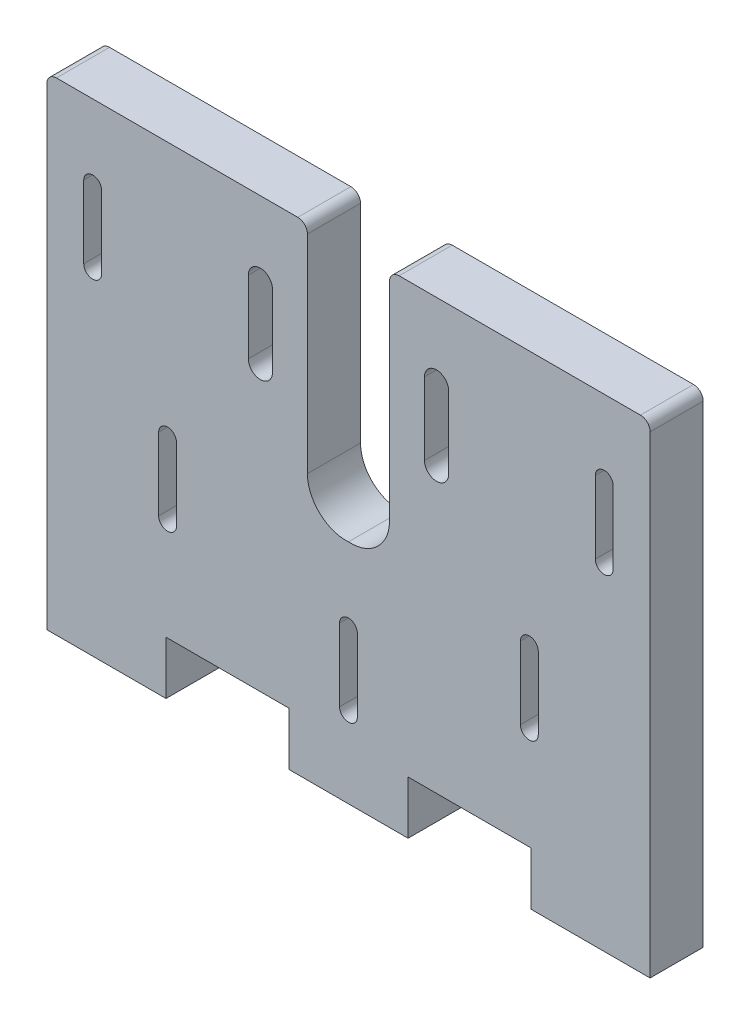
SolidWorks part; units mm, degrees
ref_plane "Front Plane" through (0, 0, 0) normal (0, 0, 1) x (1, 0, 0)
ref_plane "Top Plane" through (0, 0, 0) normal (0, 1, 0) x (1, 0, 0)
ref_plane "Right Plane" through (0, 0, 0) normal (1, 0, 0) x (0, 0, -1)
sketch "Sketch2" plane through (0, 0, 0) normal (0, 0, 1) x (1, 0, 0)
  line L1 (-0.1872, 0) -> (-0.1872, 98)
  line L9 (1.8128, 100) -> (51.8128, 100)
  line L10 (53.8128, 98) -> (53.8128, 55)
  line L12 (70.8128, 55) -> (70.8128, 98)
  line L13 (72.8128, 100) -> (122.8128, 100)
  line L14 (124.8128, 98) -> (124.8128, 0)
  line L16 (44.0628, 69.5) -> (44.0628, 84.5) construction
  line L17 (41.5628, 69.5) -> (41.5628, 84.5)
  line L18 (46.5628, 69.5) -> (46.5628, 84.5)
  line L19 (-0.1872, 0) -> (24.5128, 0)
  line L20 (80.5628, 69.5) -> (80.5628, 84.5) construction
  line L21 (83.0628, 69.5) -> (83.0628, 84.5)
  line L22 (78.0628, 69.5) -> (78.0628, 84.5)
  line L23 (24.5128, 0) -> (24.5128, 11)
  line L24 (24.5128, 11) -> (49.9628, 11)
  line L25 (49.9628, 11) -> (49.9628, 0)
  line L26 (49.9628, 0) -> (74.6628, 0)
  line L27 (74.6628, 0) -> (74.6628, 11)
  line L28 (74.6628, 11) -> (100.1128, 11)
  line L29 (100.1128, 11) -> (100.1128, 0)
  line L30 (100.1128, 0) -> (124.8128, 0)
  line L31 (9.3128, 69.5) -> (9.3128, 84.5) construction
  line L32 (7.4628, 69.5) -> (7.4628, 84.5)
  line L33 (11.1628, 69.5) -> (11.1628, 84.5)
  line L34 (24.8361, 32.0233) -> (24.8361, 47.0233) construction
  line L35 (22.9861, 32.0233) -> (22.9861, 47.0233)
  line L36 (26.6861, 32.0233) -> (26.6861, 47.0233)
  line L37 (62.3128, 16.5) -> (62.3128, 31.5) construction
  line L38 (60.4628, 16.5) -> (60.4628, 31.5)
  line L39 (64.1628, 16.5) -> (64.1628, 31.5)
  line L40 (99.7894, 32.0233) -> (99.7894, 47.0233) construction
  line L41 (97.9394, 32.0233) -> (97.9394, 47.0233)
  line L42 (101.6394, 32.0233) -> (101.6394, 47.0233)
  line L43 (115.3128, 69.5) -> (115.3128, 84.5) construction
  line L44 (113.4628, 69.5) -> (113.4628, 84.5)
  line L45 (117.1628, 69.5) -> (117.1628, 84.5)
  arc A6 (62.3128, 47.0156) -> (53.8128, 55) centre (61.8128, 55) cw
  arc A7 (62.3128, 47.0156) -> (70.8128, 55) centre (62.8128, 55) ccw
  arc A8 (53.8128, 98) -> (51.8128, 100) centre (51.8128, 98) ccw
  arc A9 (72.8128, 100) -> (70.8128, 98) centre (72.8128, 98) ccw
  arc A10 (1.8128, 100) -> (-0.1872, 98) centre (1.8128, 98) ccw
  arc A11 (124.8128, 98) -> (122.8128, 100) centre (122.8128, 98) ccw
  arc A14 (41.5628, 69.5) -> (46.5628, 69.5) centre (44.0628, 69.5) ccw
  arc A15 (46.5628, 84.5) -> (41.5628, 84.5) centre (44.0628, 84.5) ccw
  arc A16 (83.0628, 69.5) -> (78.0628, 69.5) centre (80.5628, 69.5) cw
  arc A17 (78.0628, 84.5) -> (83.0628, 84.5) centre (80.5628, 84.5) cw
  circle A23 centre (62.3128, 77) radius 53 construction
  circle A24 centre (62.3128, 24) radius 1.85 construction
  circle A25 centre (24.8361, 39.5233) radius 1.85 construction
  circle A26 centre (9.3128, 77) radius 1.85 construction
  circle A27 centre (24.8361, 114.4767) radius 1.85 [skipped]
  circle A28 centre (62.3128, 130) radius 1.85 [skipped]
  circle A29 centre (99.7894, 114.4767) radius 1.85 [skipped]
  circle A30 centre (115.3128, 77) radius 1.85 construction
  circle A31 centre (99.7894, 39.5233) radius 1.85 construction
  arc A32 (7.4628, 69.5) -> (11.1628, 69.5) centre (9.3128, 69.5) ccw
  arc A33 (11.1628, 84.5) -> (7.4628, 84.5) centre (9.3128, 84.5) ccw
  arc A34 (22.9861, 32.0233) -> (26.6861, 32.0233) centre (24.8361, 32.0233) ccw
  arc A35 (26.6861, 47.0233) -> (22.9861, 47.0233) centre (24.8361, 47.0233) ccw
  arc A36 (60.4628, 16.5) -> (64.1628, 16.5) centre (62.3128, 16.5) ccw
  arc A37 (64.1628, 31.5) -> (60.4628, 31.5) centre (62.3128, 31.5) ccw
  arc A38 (97.9394, 32.0233) -> (101.6394, 32.0233) centre (99.7894, 32.0233) ccw
  arc A39 (101.6394, 47.0233) -> (97.9394, 47.0233) centre (99.7894, 47.0233) ccw
  arc A40 (113.4628, 69.5) -> (117.1628, 69.5) centre (115.3128, 69.5) ccw
  arc A41 (117.1628, 84.5) -> (113.4628, 84.5) centre (115.3128, 84.5) ccw
  point P24 (44.0628, 77)
  point P32 (80.5628, 77)
  point P45 (62.3128, 77)
  point P46 (9.3128, 77)
  point P48 (62.3128, 0)
  point P69 (62.3128, 77)
  point P71 (24.8361, 39.5233)
  point P78 (62.3128, 24)
  point P85 (99.7894, 39.5233)
  point P92 (115.3128, 77)
  dimension "D1" = 125
  dimension "D2" = 100
  dimension "D3" = 2
  dimension "D4" = 2
  dimension "D5" = 2
  dimension "D6" = 2
  dimension "D8" = 106
  dimension "D7" = 11
  dimension "D9" = 3.7
  dimension "D10" = 8
  dimension "D11" = 24.7
  dimension "D15" = 8
  dimension "D12" = 18.25
  dimension "D13" = 17
  dimension "D14" = 18.25
  dimension "D16" = 43
  dimension "D17" = 77
  dimension "D18" = 15
  dimension "D19" = 5
  dimension "D20" = 50.15
  dimension "D22" = 3.7
extrude "Boss-Extrude7" add sketch "Sketch2" along normal blind 11
